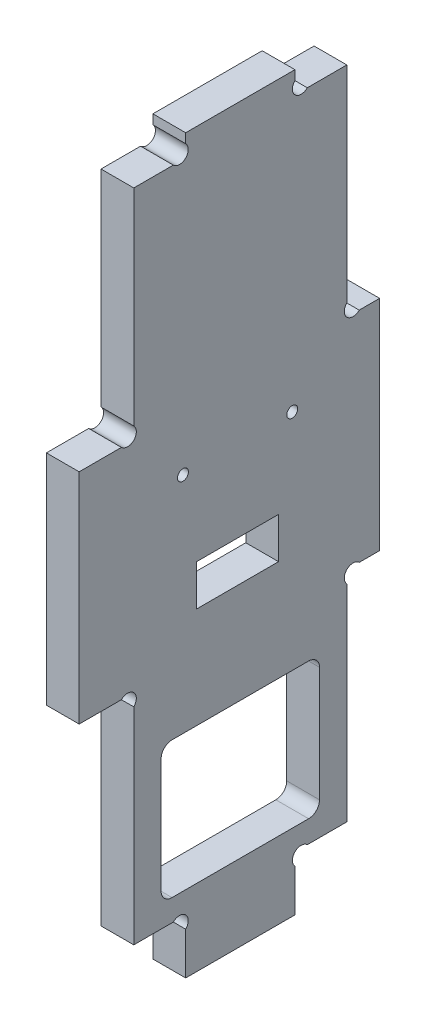
SolidWorks part; units mm, degrees
ref_plane "Plan de face" through (0, 0, 0) normal (0, 0, 1) x (1, 0, 0)
ref_plane "Plan de dessus" through (0, 0, 0) normal (0, 1, 0) x (1, 0, 0)
ref_plane "Plan de droite" through (0, 0, 0) normal (1, 0, 0) x (0, 0, -1)
sketch "Esquisse1" plane through (0, 0, 0) normal (1, 0, 0) x (0, 0, -1)
  line L13 (19.5, 7.7373) -> (19.5, 0)
  line L15 (17.2373, 10) -> (10, 10)
  line L17 (51.2627, 50) -> (55, 50)
  line L18 (7.7373, 50) -> (0, 50)
  line L19 (39.5, 7.7373) -> (39.5, 0)
  line L20 (51.2627, 90) -> (55, 90)
  line L21 (7.7373, 90) -> (0, 90)
  line L22 (19.5, 0) -> (39.5, 0)
  line L23 (41.7627, 10) -> (49, 10)
  line L24 (49, 10) -> (49, 47.7373)
  line L25 (10, 10) -> (10, 47.7373)
  line L26 (55, 90) -> (55, 50)
  line L27 (0, 50) -> (0, 90)
  line L29 (19.5, 132.2627) -> (19.5, 134)
  line L30 (39.5, 132.2627) -> (39.5, 134)
  line L31 (10, 92.2627) -> (10, 130)
  line L32 (10, 130) -> (17.2373, 130)
  line L33 (19.5, 134) -> (39.5, 134)
  line L34 (41.7627, 130) -> (49, 130)
  line L35 (49, 130) -> (49, 92.2627)
  arc A0 (51.2627, 50) -> (49, 47.7373) centre (50.1314, 48.8686) ccw
  arc A1 (10, 47.7373) -> (7.7373, 50) centre (8.8686, 48.8686) ccw
  arc A2 (19.5, 7.7373) -> (17.2373, 10) centre (18.3686, 8.8686) ccw
  arc A3 (39.5, 7.7373) -> (41.7627, 10) centre (40.6314, 8.8686) cw
  arc A4 (10, 92.2627) -> (7.7373, 90) centre (8.8686, 91.1314) cw
  arc A5 (51.2627, 90) -> (49, 92.2627) centre (50.1314, 91.1314) cw
  arc A6 (17.2373, 130) -> (19.5, 132.2627) centre (18.3686, 131.1314) ccw
  arc A7 (41.7627, 130) -> (39.5, 132.2627) centre (40.6314, 131.1314) cw
  point P1 (13.6186, 10)
  dimension "D14" = 1.1314
  dimension "D15" = 1.1314
  dimension "D17" = 1.1314
  dimension "D23" = 1.1314
  dimension "D10" = 1.6
  dimension "D1" = 6
  dimension "D2" = 10
  dimension "D3" = 9.5
  dimension "D4" = 9.5
  dimension "D5" = 10
  dimension "D6" = 40
  dimension "D7" = 40
  dimension "D8" = 40
  dimension "D9" = 4
  dimension "D11" = 1.1314
  dimension "D12" = 1.1314
  dimension "D13" = 1.1314
  dimension "D16" = 20
  dimension "D18" = 1.1314
  dimension "D19" = 1.1314
  dimension "D20" = 1.1314
  dimension "D21" = 1.1314
  dimension "D22" = 1.1314
  dimension "D24" = 3.7373
  dimension "D25" = 1.7373
  dimension "D26" = 1.1314
  dimension "D27" = 7.2373
  dimension "D28" = 1.1314
  dimension "D29" = 1.7373
  dimension "D30" = 20
  dimension "D31" = 39
  dimension "D32" = 39
extrude "Extrusion1" add sketch "Esquisse1" along normal blind 6
sketch "Esquisse2" plane through (0, 0, 0) normal (-1, 0, 0) x (0, 0, 1)
  line L0 (-49, 10) -> (-49, 47.7373) construction
  line L1 (-10, 10) -> (-17.2373, 10) construction
  line L2 (-10, 47.7373) -> (-10, 10) construction
  line L3 (-41.7627, 10) -> (-49, 10) construction
  line L4 (-15, 39) -> (-44, 39)
  line L5 (-15, 39) -> (-15, 14)
  line L6 (-15, 14) -> (-44, 14)
  line L7 (-44, 39) -> (-44, 14)
  line L8 (-49, 10) -> (-49, 47.7373) construction
  line L9 (-10, 47.7373) -> (-10, 10) construction
  circle A0 centre (-39, 80) radius 1
  circle A1 centre (-19, 80) radius 1
  dimension "D1" = 2
  dimension "D2" = 10
  dimension "D3" = 20
  dimension "D4" = 9
  dimension "D5" = 70
  dimension "D6" = 4
  dimension "D7" = 5
  dimension "D8" = 5
  dimension "D9" = 25
extrude "Enlèv. mat.-Extru.1" cut sketch "Esquisse2" against normal through all
fillet "Congé1" radius 2 4 edges at (3, 14, -44) (3, 14, -15) (3, 39, -15) (3, 39, -44)
sketch "Esquisse3" plane through (0, 0, 0) normal (-1, 0, 0) x (0, 0, 1)
  line L1 (-36.5, 65) -> (-21.5, 65)
  line L2 (-36.5, 65) -> (-36.5, 57.5)
  line L3 (-36.5, 57.5) -> (-21.5, 57.5)
  line L4 (-21.5, 65) -> (-21.5, 57.5)
  circle A0 centre (-39, 80) radius 1 construction
  circle A1 centre (-19, 80) radius 1 construction
  dimension "D1" = 15
  dimension "D2" = 7.5
  dimension "D3" = 2.5
  dimension "D4" = 2.5
  dimension "D5" = 15
extrude "Enlèv. mat.-Extru.2" cut sketch "Esquisse3" against normal through all
